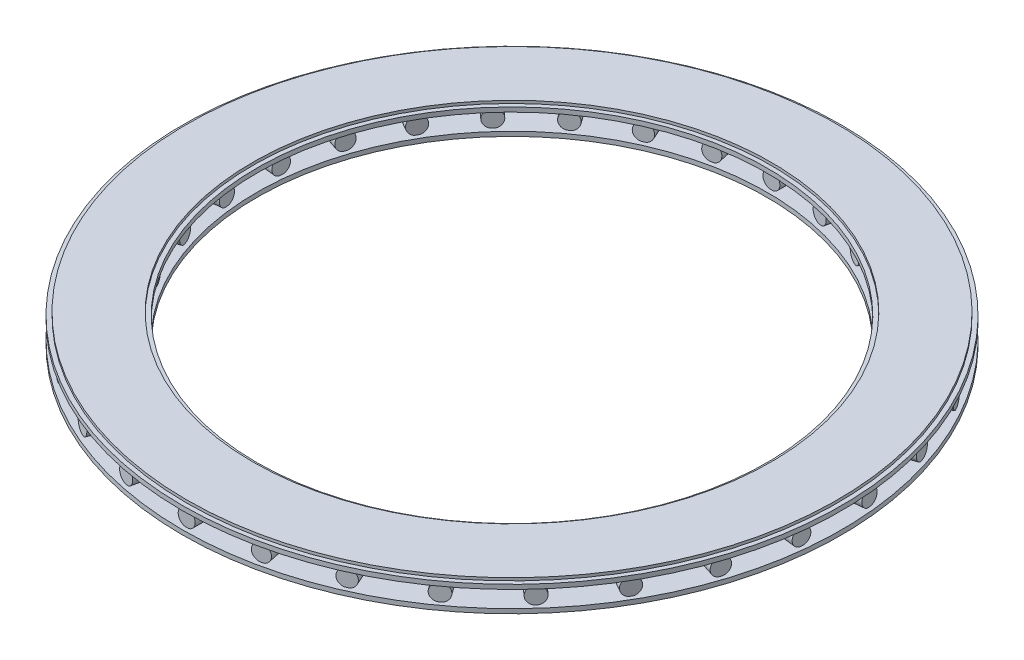
SolidWorks part; units mm, degrees
ref_plane "Front Plane" through (0, 0, 0) normal (0, 0, 1) x (1, 0, 0)
ref_plane "Top Plane" through (0, 0, 0) normal (0, 1, 0) x (1, 0, 0)
ref_plane "Right Plane" through (0, 0, 0) normal (1, 0, 0) x (0, 0, -1)
sketch "Sketch1" plane through (0, 0, 0) normal (0, 1, 0) x (1, 0, 0)
  circle A0 centre (0, 0) radius 60
  circle A1 centre (0, 0) radius 77.5
  dimension "D1" = 155
  dimension "D2" = 120
sketch "Sketch2" plane through (0, 0, 0) normal (0, 1, 0) x (1, 0, 0)
  line L0 (0, 0) -> (0, -77.5) construction
  line L2 (0, -61) -> (-2, -61)
  line L3 (0, -61) -> (0, -76.5)
  line L4 (0, -76.5) -> (-2, -76.5)
  line L5 (-2, -61) -> (-2, -76.5)
  circle A0 centre (0, 0) radius 77.5 construction
  circle A1 centre (0, 0) radius 60 construction
  dimension "D1" = 4
  dimension "D2" = 1
  dimension "D3" = 1
revolve "Revolve1" add sketch "Sketch2" angle 360 about L0
sketch "Sketch3" plane through (0, 0, 0) normal (1, 0, 0) x (0, 0, -1)
  line L0 (0, 0) -> (0, 36.2157) construction
pattern_circular "CirPattern2" count 30 over 360 about axis through (0, 0, 0) along (0, 1, 0) of bodies 101
ref_plane "Plane1" through (0, 1.95, 0) normal (0, 1, 0) x (1, 0, 0)
sketch "Sketch4" plane through (0, 1.95, 0) normal (0, 1, 0) x (1, 0, 0)
  circle A1 centre (0, 0) radius 77.5
  circle A2 centre (0, 0) radius 77.5
  circle A3 centre (0, 0) radius 60
  circle A4 centre (0, 0) radius 60
  dimension "D1" = 0
  dimension "D2" = 0
extrude "Boss-Extrude1" add sketch "Sketch4" along normal blind 1.05
ref_plane "Plane2" through (0, -1.95, 0) normal (0, 1, 0) x (1, 0, 0)
sketch "Sketch5" plane through (0, -1.95, 0) normal (0, 1, 0) x (1, 0, 0)
  circle A1 centre (0, 0) radius 77.5
  circle A2 centre (0, 0) radius 77.5
  circle A3 centre (0, 0) radius 60
  circle A4 centre (0, 0) radius 60
  dimension "D1" = 0
  dimension "D2" = 0
extrude "Boss-Extrude2" add sketch "Sketch5" against normal blind 1.05
sketch "Sketch6" plane through (0, 3, 0) normal (0, 1, 0) x (1, 0, 0)
  circle A2 centre (0, 0) radius 61
  circle A3 centre (0, 0) radius 61
  circle A5 centre (0, 0) radius 76.5
  circle A6 centre (0, 0) radius 76.5
  dimension "D1" = 1
  dimension "D2" = 1
extrude "Boss-Extrude3" add sketch "Sketch6" along normal blind 0.65 separate body
